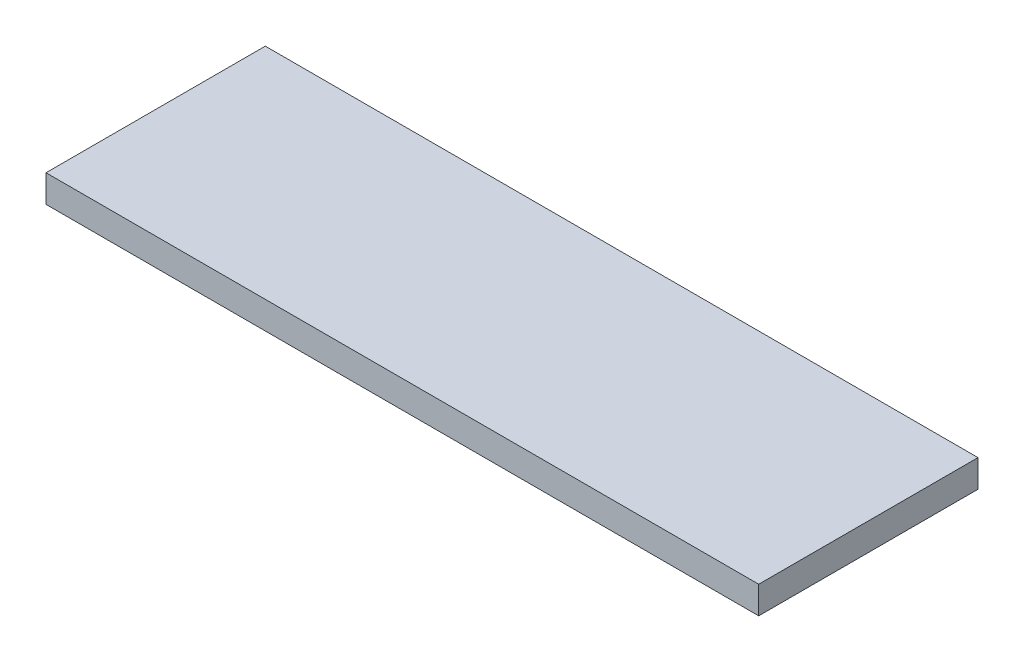
SolidWorks part; units mm, degrees
ref_plane "Front Plane" through (0, 0, 0) normal (0, 0, 1) x (1, 0, 0)
ref_plane "Top Plane" through (0, 0, 0) normal (0, 1, 0) x (1, 0, 0)
ref_plane "Right Plane" through (0, 0, 0) normal (1, 0, 0) x (0, 0, -1)
sketch "Sketch1" plane through (0, 0, 0) normal (0, 1, 0) x (1, 0, 0)
  line L1 (-60.3434, 83.2944) -> (269.8566, 83.2944)
  line L2 (-60.3434, 83.2944) -> (-60.3434, -18.3056)
  line L3 (-60.3434, -18.3056) -> (269.8566, -18.3056)
  line L4 (269.8566, 83.2944) -> (269.8566, -18.3056)
  dimension "D1" = 101.6
  dimension "D2" = 330.2
extrude "Boss-Extrude1" add sketch "Sketch1" along normal blind 12.7
